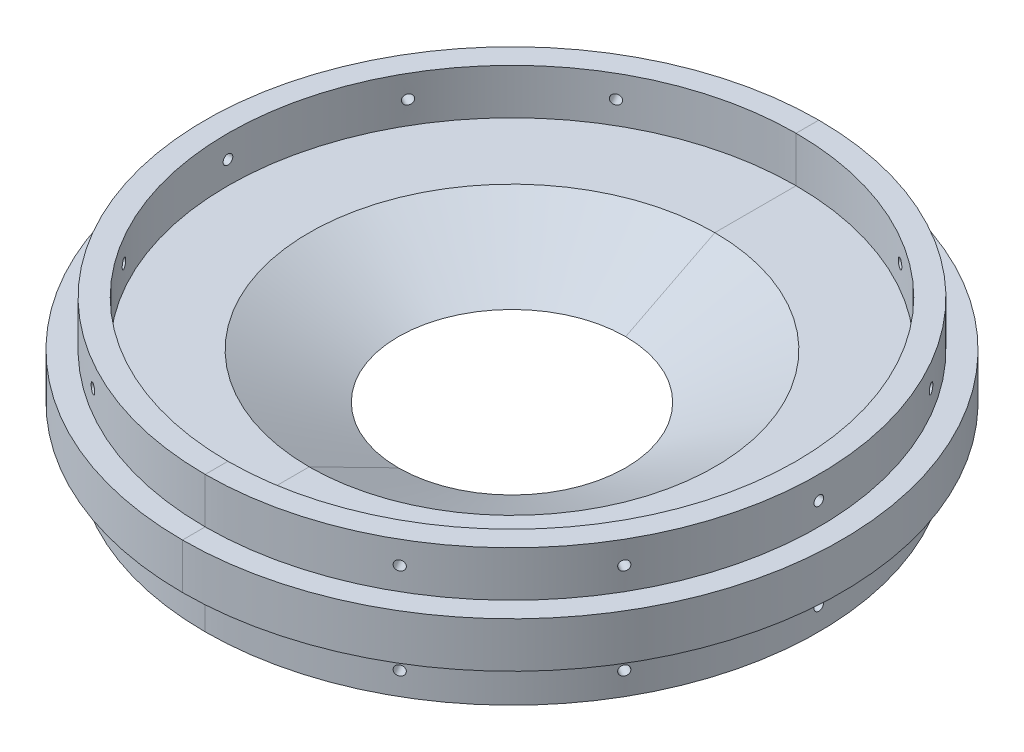
SolidWorks part; units mm, degrees
ref_plane "Front Plane" through (0, 0, 0) normal (0, 0, 1) x (1, 0, 0)
ref_plane "Top Plane" through (0, 0, 0) normal (0, 1, 0) x (1, 0, 0)
ref_plane "Right Plane" through (0, 0, 0) normal (1, 0, 0) x (0, 0, -1)
sketch "Sketch1" plane through (0, 0, 0) normal (0, 1, 0) x (1, 0, 0)
  circle A0 centre (0, 0) radius 92.075
  circle A1 centre (0, 0) radius 31.75
  dimension "D1" = 184.15
  dimension "D2" = 63.5
extrude "Boss-Extrude1" add sketch "Sketch1" along normal mid plane 12.7
sketch "Sketch5" plane through (0, 6.35, 0) normal (0, 1, 0) x (1, 0, 0)
  circle A0 centre (0, 0) radius 85.725
  circle A1 centre (0, 0) radius 79.375
  dimension "D1" = 171.45
  dimension "D2" = 158.75
extrude "Boss-Extrude2" add sketch "Sketch5" along normal blind 12.7
ref_plane "Plane1" through (0, 0, -85.725) normal (0, 0, -1) x (-1, 0, 0)
sketch "Sketch6" plane through (0, 0, -85.725) normal (0, 0, -1) x (-1, 0, 0)
  line L0 (0, 13.97) -> (0, -13.97) construction
  line L1 (92.075, 6.35) -> (-92.075, 6.35) construction
  circle A0 centre (0, 12.7) radius 1.3525
  dimension "D1" = 2.7051
  dimension "D2" = 6.35
extrude "Cut-Extrude1" cut sketch "Sketch6" against normal blind 12.7
pattern_circular "CirPattern1" count 12 over 360 about axis through (0, 6.35, 0) along (0, -1, 0) of "Cut-Extrude1"
mirror "Mirror1" about plane through (0, 0, 0) normal (0, 1, 0) of "CirPattern1", "Cut-Extrude1", "Boss-Extrude2"
sketch "Sketch7" plane through (0, 19.05, 0) normal (0, 1, 0) x (1, 0, 0)
  line L0 (-25.7878, 75.0692) -> (-28.1663, 80.9657)
  line L1 (28.1663, 80.9657) -> (25.7878, 75.0692)
  arc A0 (28.1663, 80.9657) -> (-28.1663, 80.9657) centre (0, 0) ccw
  circle A1 centre (0, 0) radius 85.725 construction
  arc A2 (25.7878, 75.0692) -> (-25.7878, 75.0692) centre (0, 0) ccw
  circle A3 centre (0, 0) radius 79.375 construction
extrude "Boss-Extrude3" add sketch "Sketch7" against normal up to surface (25.4 mm away)
mirror "Mirror3" about plane through (0, 0, 0) normal (0, 1, 0) of "Boss-Extrude3"
mirror "Mirror4" about plane through (0, 0, 0) normal (0, 0, 1) of "Boss-Extrude3"
mirror "Mirror5" about plane through (0, 0, 0) normal (0, 1, 0) of "Mirror4"
sketch "Sketch4" plane through (0, 0, 0) normal (0, 0, 1) x (1, 0, 0)
  line L0 (0, 23.2786) -> (0, -14.9525) construction
sketch "Sketch3" plane through (0, 0, 0) normal (0, 0, 1) x (1, 0, 0)
  line L0 (-31.75, -6.35) -> (-56.6752, 6.35)
  line L1 (92.075, 6.35) -> (-92.075, 6.35) construction
  line L2 (-56.6752, 6.35) -> (-31.75, 6.35)
  line L3 (-31.75, 6.35) -> (-31.75, -6.35)
  line L4 (-31.75, -6.35) -> (31.75, -6.35) construction
  line L5 (31.75, 6.35) -> (-31.75, 6.35) construction
  dimension "D1" = 27
revolve "Cut-Revolve1" cut sketch "Sketch3" angle 360 about L0
split "Split1" trim tools "Right Plane" bodies to split 103 resulting bodies 115 116
